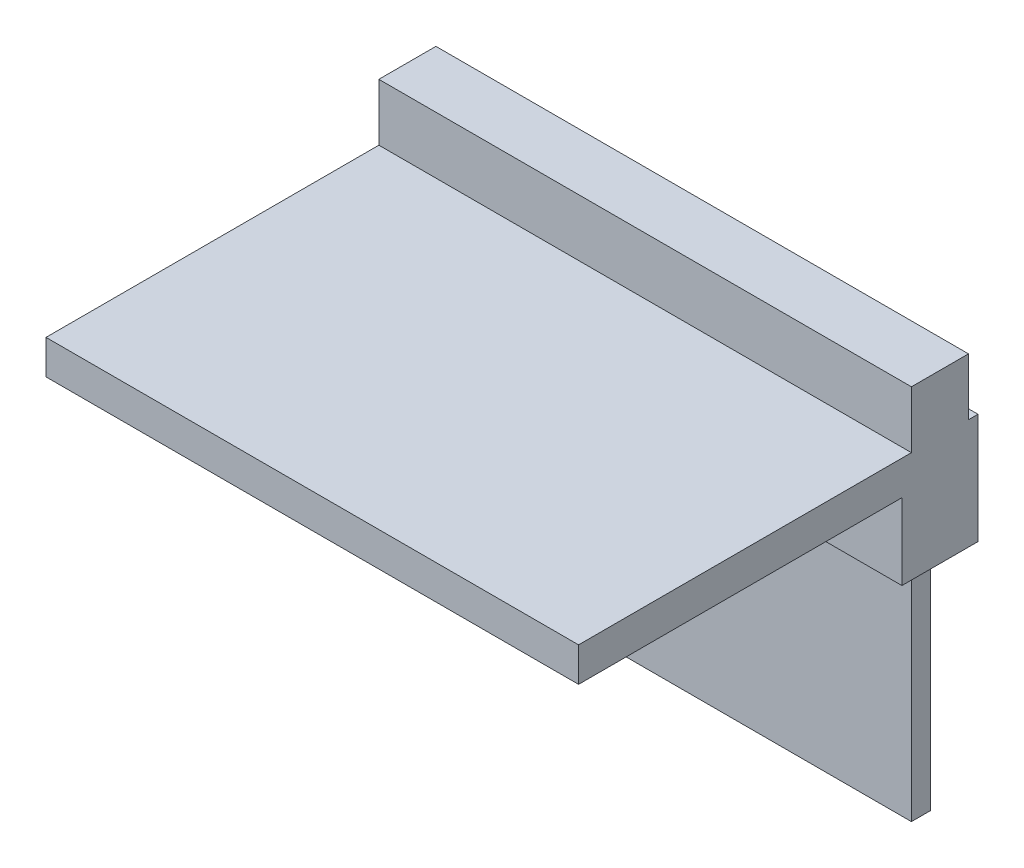
SolidWorks part; units mm, degrees
ref_plane "Спереди" through (0, 0, 0) normal (0, 0, 1) x (1, 0, 0)
ref_plane "Сверху" through (0, 0, 0) normal (0, 1, 0) x (1, 0, 0)
ref_plane "Справа" through (0, 0, 0) normal (1, 0, 0) x (0, 0, -1)
sketch "Эскиз1" plane through (0, 0, 0) normal (0, 1, 0) x (1, 0, 0)
  line L1 (-7, -5.25) -> (7, -5.25)
  line L2 (-7, -5.25) -> (-7, 5.25)
  line L3 (-7, 5.25) -> (7, 5.25)
  line L4 (7, -5.25) -> (7, 5.25)
  line L5 (-7, -5.25) -> (7, 5.25) construction
  line L6 (-7, 5.25) -> (7, -5.25) construction
  point P0 (0, 0)
  dimension "D1" = 14
  dimension "D2" = 10.5
extrude "Бобышка-Вытянуть1" add sketch "Эскиз1" along normal blind 0.9
sketch "Эскиз3" plane through (0, 0, 0) normal (0, -1, 0) x (1, 0, 0)
  line L0 (7, 5.25) -> (7, -5.25) construction
  line L1 (-7, -5.25) -> (7, -5.25)
  line L2 (-7, -5.25) -> (-7, -3.25)
  line L3 (-7, -3.25) -> (7, -3.25)
  line L4 (7, -5.25) -> (7, -3.25)
  dimension "D1" = 2
extrude "Бобышка-Вытянуть2" add sketch "Эскиз3" along normal blind 2
sketch "Эскиз4" plane through (0, -2, 0) normal (0, -1, 0) x (1, 0, 0)
  line L0 (0, 4.6207) -> (0, -6.1977) construction
  line L1 (6.5, -4.5) -> (-6.5, -4.5)
  line L2 (6.5, -4.5) -> (6.5, -4)
  line L3 (6.5, -4) -> (-6.5, -4)
  line L4 (-6.5, -4.5) -> (-6.5, -4)
  line L5 (6.5, -4.5) -> (-6.5, -4) construction
  line L6 (6.5, -4) -> (-6.5, -4.5) construction
  line L7 (7, -3.25) -> (-7, -3.25) construction
  point P0 (0, -4.25)
  dimension "D1" = 13
  dimension "D2" = 0.5
  dimension "D3" = 0.75
extrude "Бобышка-Вытянуть3" add sketch "Эскиз4" along normal blind 6
sketch "Эскиз8" plane through (0, 0.9, 0) normal (0, 1, 0) x (1, 0, 0)
  line L6 (7, 3.5) -> (-7, 3.5)
  line L7 (7, 3.5) -> (7, 5)
  line L8 (7, 5) -> (-7, 5)
  line L9 (-7, 3.5) -> (-7, 5)
  line L10 (7, 3.5) -> (-7, 5) construction
  line L11 (7, 5) -> (-7, 3.5) construction
  point P0 (0, 4.25)
  dimension "D1" = 1.5
  dimension "D2" = 14
extrude "Бобышка-Вытянуть4" add sketch "Эскиз8" along normal blind 1.5
